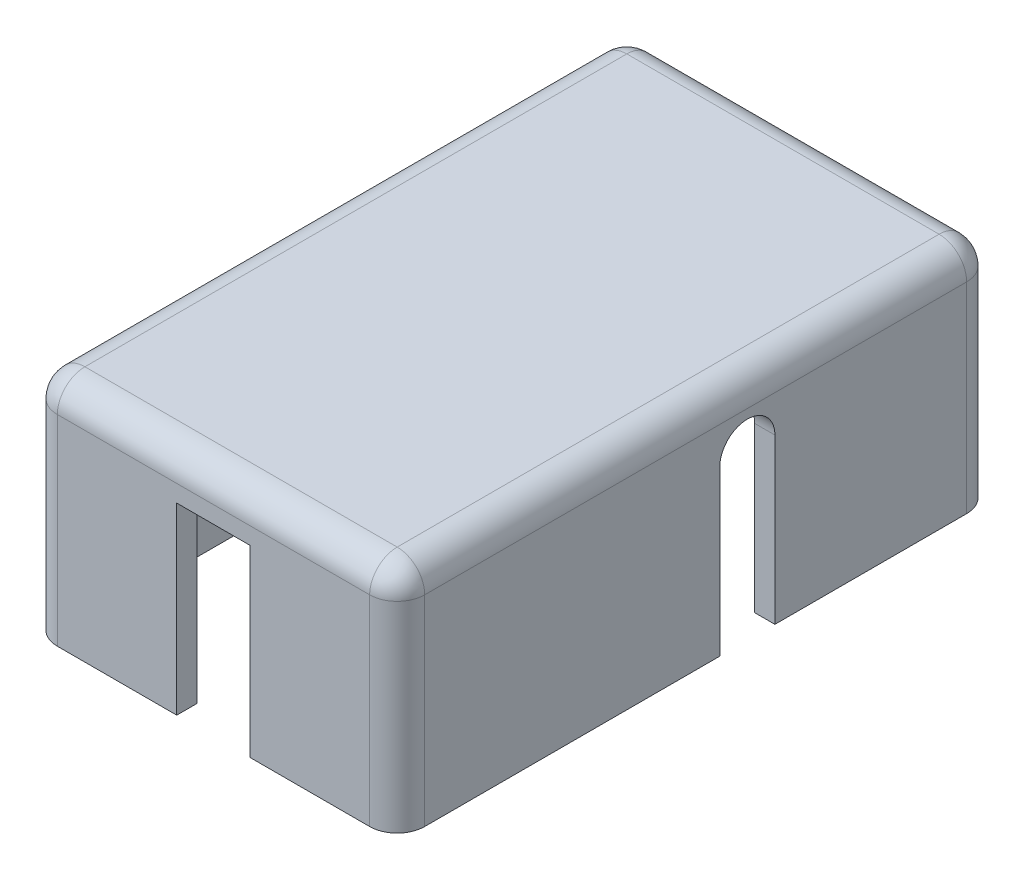
SolidWorks part; units mm, degrees
ref_plane "Front Plane" through (0, 0, 0) normal (0, 0, 1) x (1, 0, 0)
ref_plane "Top Plane" through (0, 0, 0) normal (0, 1, 0) x (1, 0, 0)
ref_plane "Right Plane" through (0, 0, 0) normal (1, 0, 0) x (0, 0, -1)
ref_plane "Plane1" through (0, 0, 0) normal (0, -1, 0) x (-1, 0, 0)
sketch "Sketch2" plane through (0, 0, 0) normal (0, -1, 0) x (-1, 0, 0)
  line L0 (17.5, -30) -> (-17.5, -30) construction
  line L5 (17.5, 30) -> (17.5, -30) construction
  line L6 (-17.5, -30) -> (-17.5, 30) construction
  line L7 (-17.5, 30) -> (17.5, 30) construction
  line L8 (17.5, -30) -> (-17.5, -30) construction
  line L9 (17.5, 30) -> (17.5, -30) construction
  line L10 (-17.5, -30) -> (-17.5, 30) construction
  line L11 (-17.5, 30) -> (17.5, 30) construction
  line L12 (20, 32.5) -> (20, -32.5)
  line L13 (20, -32.5) -> (-20, -32.5)
  line L14 (-20, -32.5) -> (-20, 32.5)
  line L15 (-20, 32.5) -> (20, 32.5)
  line L16 (17.8, -30.3) -> (-17.8, -30.3)
  line L17 (-17.8, -30.3) -> (-17.8, 30.3)
  line L18 (-17.8, 30.3) -> (17.8, 30.3)
  line L19 (17.8, 30.3) -> (17.8, -30.3)
  dimension "D1" = 2.5
  dimension "D2" = 0.3
extrude "Boss-Extrude1" add sketch "Sketch2" against normal up to surface (21.85 mm away)
ref_plane "Plane2" through (0, 21.85, 0) normal (0, 1, 0) x (1, 0, 0)
sketch "Sketch9" plane through (20, 0, 0) normal (1, 0, 0) x (0, 0, -1)
  line L0 (-4.3538, 17.85) -> (12.112, 17.85) construction
  line L1 (2.6236, 17.85) -> (2.6236, 0)
  line L2 (32.5, 0) -> (-32.5, 0) construction
  line L3 (2.6236, 0) -> (8.6236, 0)
  line L4 (8.6236, 21.85) -> (2.6236, 21.85)
  line L5 (2.6236, 21.85) -> (2.6236, 5.39)
  line L6 (2.6236, 5.39) -> (8.6236, 5.39)
  line L7 (8.6236, 5.39) -> (8.6236, 21.85)
  line L8 (8.6236, 21.85) -> (2.6236, 21.85) construction
  line L9 (2.6236, 21.85) -> (2.6236, 5.39) construction
  line L11 (8.6236, 5.39) -> (8.6236, 21.85) construction
  line L12 (8.6236, 0) -> (8.6236, 17.85)
  circle A0 centre (5.6236, 17.85) radius 2 construction
  circle A1 centre (5.6236, 17.85) radius 2 construction
  arc A2 (2.6236, 17.85) -> (8.6236, 17.85) centre (5.6236, 17.85) cw
  dimension "D2" = 3
  dimension "D1" = 0
extrude "Cut-Extrude1" cut sketch "Sketch9" against normal up to surface (37.8 mm away)
mirror "Mirror1" about plane through (0, 0, 0) normal (1, 0, 0) of "Cut-Extrude1"
sketch "Sketch10" plane through (0, 0, -32.5) normal (0, 0, -1) x (-1, 0, 0)
  line L0 (-10.01, 7.195) -> (-10.01, 17.945) construction
  line L1 (-12.885, 20.07) -> (-7.885, 20.07)
  line L2 (-12.885, 20.07) -> (-12.885, 5.07)
  line L3 (-12.885, 5.07) -> (-7.885, 5.07)
  line L4 (-7.885, 20.07) -> (-7.885, 5.07)
  line L5 (-10.01, 17.945) -> (-10.76, 17.945) construction
  line L6 (20, 0) -> (-20, 0) construction
  line L7 (0.645, 0) -> (7.645, 0)
  line L8 (20, 21.85) -> (-20, 21.85) construction
  line L10 (0.645, 20.35) -> (0.645, 0)
  line L14 (0.645, 20.35) -> (7.645, 20.35)
  line L15 (7.645, 20.35) -> (7.645, 0)
  circle A0 centre (4.145, 16.945) radius 1.5 construction
  circle A1 centre (4.145, 8.195) radius 1.5 construction
  circle A2 centre (4.145, 16.945) radius 1.5 construction
  circle A3 centre (4.145, 8.195) radius 1.5 construction
  point P6 (-10.01, 12.57)
  point P7 (-7.885, 12.57)
  point P8 (-10.385, 20.07)
  point P11 (-10.385, 17.945)
  point P18 (4.145, 20.35)
  dimension "D1" = 5
  dimension "D2" = 15
  dimension "D4" = 1.5
  dimension "D5" = 7
extrude "Cut-Extrude2" cut sketch "Sketch10" against normal up to surface (2.2 mm away) up to face at (0, 10.925, -30.3)
sketch "Sketch11" plane through (0, 0, 32.5) normal (0, 0, 1) x (1, 0, 0)
  line L0 (2.86, 18.75) -> (2.22, 18.75) construction
  line L1 (-0.32, 16.75) -> (0.32, 16.75) construction
  line L2 (0.32, 18.75) -> (-0.32, 18.75) construction
  line L3 (-2.22, 18.75) -> (-2.86, 18.75) construction
  line L4 (2.86, 18.75) -> (2.22, 18.75)
  line L5 (-0.32, 16.75) -> (0.32, 16.75)
  line L6 (0.32, 18.75) -> (-0.32, 18.75)
  line L7 (-2.22, 18.75) -> (-2.86, 18.75)
  line L8 (20, 0) -> (-20, 0) construction
  line L9 (-4, 20) -> (4, 20)
  line L10 (-4, 20) -> (-4, 0)
  line L11 (-4, 0) -> (4, 0)
  line L12 (4, 20) -> (4, 0)
  point P14 (0, 20)
  dimension "D1" = 20
  dimension "D2" = 8
extrude "Cut-Extrude3" cut sketch "Sketch11" against normal up to surface (2.2 mm away)
sketch "Sketch8" plane through (0, 21.85, 0) normal (0, 1, 0) x (1, 0, 0)
  line L0 (20, -32.5) -> (20, 32.5) construction
  line L1 (-20, 32.5) -> (20, 32.5)
  line L2 (-20, 32.5) -> (-20, -32.5)
  line L3 (-20, -32.5) -> (20, -32.5)
  line L4 (20, 32.5) -> (20, -32.5)
  line L5 (20, 32.5) -> (20, -32.5) construction
  line L6 (20, -32.5) -> (-20, -32.5) construction
extrude "Boss-Extrude2" add sketch "Sketch8" along normal blind 3
fillet "Fillet1" radius 3 8 edges at (0, 24.85, -32.5) (20, 24.85, 0) (0, 24.85, 32.5) (-20, 24.85, 0) (20, 12.425, -32.5) (-20, 12.425, -32.5) (20, 12.425, 32.5) (-20, 12.425, 32.5)
